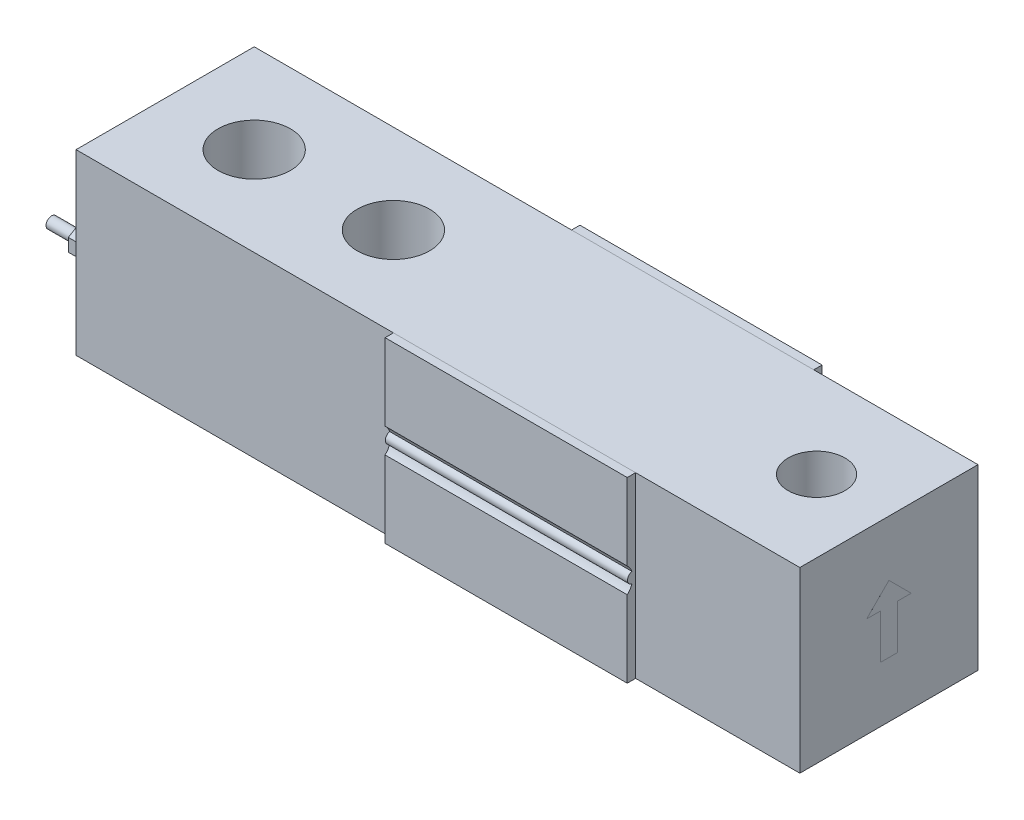
SolidWorks part; units mm, degrees
material "Ст 3 ГОСТ 380-2005"
ref_plane "Спереди" through (0, 0, 0) normal (0, 0, 1) x (1, 0, 0)
ref_plane "Сверху" through (0, 0, 0) normal (0, 1, 0) x (1, 0, 0)
ref_plane "Слева" through (0, 0, 0) normal (1, 0, 0) x (0, 0, -1)
sketch "Эскиз1" plane through (0, 0, 0) normal (0, 1, 0) x (1, 0, 0)
  line L0 (-117, 0) -> (0, 0) construction
  line L1 (-117, -16) -> (13, -16)
  line L2 (-117, -16) -> (-117, 16)
  line L3 (-117, 16) -> (13, 16)
  line L4 (13, -16) -> (13, 16)
  dimension "D1" = 13
  dimension "D2" = 130
  dimension "D3" = 32
extrude "Вытянуть1" add sketch "Эскиз1" along normal blind 32
sketch "Эскиз2" plane through (-117, 0, 0) normal (-1, 0, 0) x (0, 0, 1)
  line L0 (-16, 32) -> (16, 32) construction
  line L1 (-16, 0) -> (-17.5, 0)
  line L2 (-16, 0) -> (-16, 32)
  line L3 (-16, 32) -> (-17.5, 32)
  line L4 (-17.5, 0) -> (-17.5, 13.7639)
  line L5 (-16, 16) -> (-24.0214, 16) construction
  line L6 (-17.5, 18.2361) -> (-17.5, 32)
  line L7 (0, 0) -> (0, 15.0231) construction
  line L8 (16, 16) -> (24.0214, 16) construction
  line L9 (17.5, 18.2361) -> (17.5, 32)
  line L10 (17.5, 0) -> (17.5, 13.7639)
  line L11 (16, 32) -> (17.5, 32)
  line L12 (16, 0) -> (16, 32)
  line L13 (16, 0) -> (17.5, 0)
  arc A0 (-17.5, 18.2361) -> (-17.5, 13.7639) centre (-19.5, 16) cw construction
  arc A1 (-16.6635, 16.9769) -> (-16.6635, 15.0231) centre (-16.45, 16) ccw
  arc A2 (-17.5, 13.7639) -> (-16.6635, 15.0231) centre (-19.5, 16) ccw
  arc A3 (-17.5, 18.2361) -> (-16.6635, 16.9769) centre (-19.5, 16) cw
  arc A4 (17.5, 18.2361) -> (17.5, 13.7639) centre (19.5, 16) ccw construction
  arc A5 (17.5, 18.2361) -> (16.6635, 16.9769) centre (19.5, 16) ccw
  arc A6 (17.5, 13.7639) -> (16.6635, 15.0231) centre (19.5, 16) cw
  arc A7 (16.6635, 16.9769) -> (16.6635, 15.0231) centre (16.45, 16) cw
  dimension "D4" = 3
  dimension "D5" = 1
  dimension "D1" = 1.5
  dimension "D2" = 0.5
  dimension "D3" = 0.05
extrude "Вытянуть2" add sketch "Эскиз2" against normal blind 43.5 from offset 57 separate body offset against normal yes
sketch "Эскиз3" plane through (0, 32, 0) normal (0, 1, 0) x (1, 0, 0)
  line L0 (0, 0) -> (-101, 0) construction
  line L1 (-117, 16) -> (-117, -16) construction
  circle A0 centre (-101, 0) radius 6.5
  circle A1 centre (-76, 0) radius 6.5
  dimension "D1" = 13
  dimension "D2" = 25
  dimension "D3" = 16
extrude "Вытянуть3" cut sketch "Эскиз3" against normal through all
hole_wizard "Отверстие обработанное метчиком M12x1.751" positions "Эскиз5" profile "Эскиз4" tap size "M12x1.75" standard "ГОСТ" end condition through all
sketch "Эскиз5" plane through (0, 32, 0) normal (0, 1, 0) x (-1, 0, 0)
  line L0 (117, 16) -> (-13, 16) construction
  line L1 (-13, 16) -> (-13, -16) construction
  circle A0 centre (76, 0) radius 6.5 construction
  point P0 (0, 0)
  dimension "D3" = 76
  dimension "D1" = 16
  dimension "D2" = 13
sketch "Эскиз4" plane through (0, 32, 0) normal (1, 0, 0) x (0, 0, 1)
  line L0 (0, 0) -> (0, 32)
  line L1 (0, 32) -> (5.1, 32)
  line L2 (5.1, 32) -> (5.1, 0)
  line L5 (5.1, 0) -> (0, 0)
  line L11 (0, -6.35) -> (0, 107.95) construction
  dimension "Диаметр проходного сверла" = 10.2
  dimension "Глубина проходного сверла" = 32
cosmetic thread "Отверстие резьбы1" parameters "D2"=12
sketch "Эскиз6" plane through (-117, 0, 0) normal (-1, 0, 0) x (0, 0, 1)
  line L1 (13.5, 16) -> (16, 16) construction
  line L2 (16, 32) -> (16, 0) construction
  circle A0 centre (13.5, 16) radius 1.5
  dimension "D1" = 3
  dimension "D2" = 2.5
extrude "Вытянуть4" add sketch "Эскиз6" along normal blind 0.3
sketch "Эскиз7" plane through (-117.3, 0, 0) normal (-1, 0, 0) x (0, 0, 1)
  line L1 (13.5, 18.3094) -> (11.5, 17.1547)
  line L2 (11.5, 17.1547) -> (11.5, 14.8453)
  line L3 (11.5, 14.8453) -> (13.5, 13.6906)
  line L4 (13.5, 13.6906) -> (15.5, 14.8453)
  line L5 (15.5, 14.8453) -> (15.5, 17.1547)
  line L6 (15.5, 17.1547) -> (13.5, 18.3094)
  circle A0 centre (13.5, 16) radius 2.3094 construction
  dimension "D1" = 4
extrude "Вытянуть5" add sketch "Эскиз7" along normal blind 1.6
sketch "Эскиз8" plane through (-118.9, 0, 0) normal (-1, 0, 0) x (0, 0, 1)
  circle A0 centre (13.5, 16) radius 1
  circle A1 centre (13.5, 16) radius 1.5 construction
  dimension "D1" = 2
extrude "Вытянуть6" add sketch "Эскиз8" along normal blind 5
sketch "Эскиз10" plane through (13, 0, 0) normal (1, 0, 0) x (0, 0, -1)
  line L0 (0, 22) -> (0, 10) construction
  line L1 (-16, 0) -> (16, 0) construction
  line L14 (0, 22) -> (-4, 18)
  line L15 (-4, 18) -> (-1.5, 18)
  line L16 (-1.5, 18) -> (-1.5, 10)
  line L17 (-1.5, 10) -> (1.5, 10)
  line L18 (1.5, 10) -> (1.5, 18)
  line L19 (1.5, 18) -> (4, 18)
  line L20 (4, 18) -> (0, 22)
  point P10 (0, 16)
  dimension "D1" = 16
  dimension "D2" = 45
  dimension "D3" = 3
  dimension "D4" = 8
  dimension "D5" = 4
  dimension "D6" = 12
extrude "Вытянуть8" add sketch "Эскиз10" along normal blind 0.002
